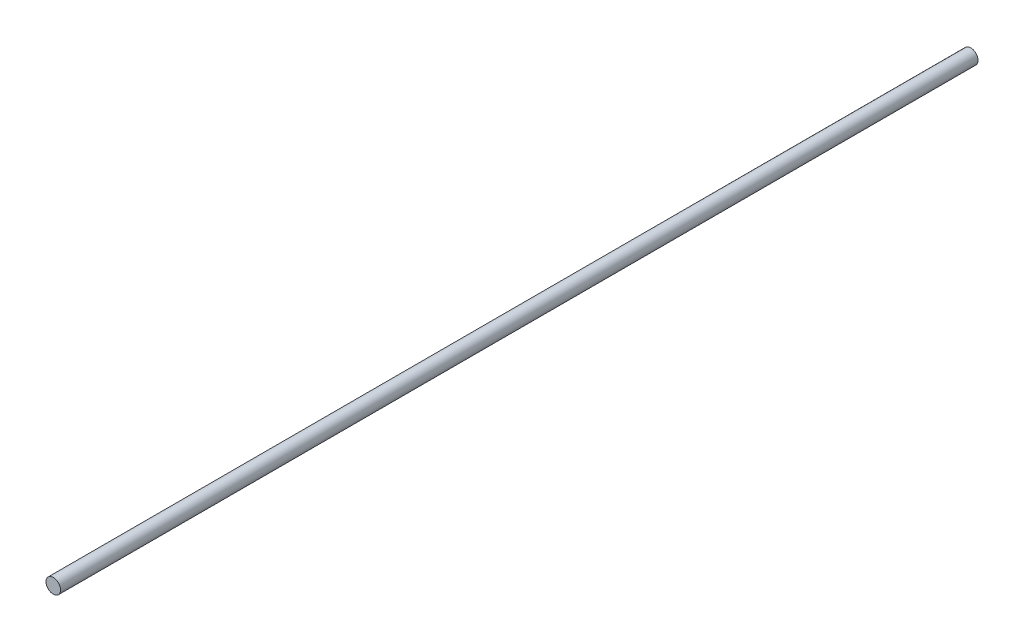
SolidWorks part; units mm, degrees
ref_plane "Front Plane" through (0, 0, 0) normal (0, 0, 1) x (1, 0, 0)
ref_plane "Top Plane" through (0, 0, 0) normal (0, 1, 0) x (1, 0, 0)
ref_plane "Right Plane" through (0, 0, 0) normal (1, 0, 0) x (0, 0, -1)
sketch "Sketch1" plane through (0, 0, 0) normal (0, 0, 1) x (1, 0, 0)
  circle A0 centre (0, 0) radius 3.9688
  dimension "D1" = 7.9375
extrude "Boss-Extrude1" add sketch "Sketch1" along normal blind 500
